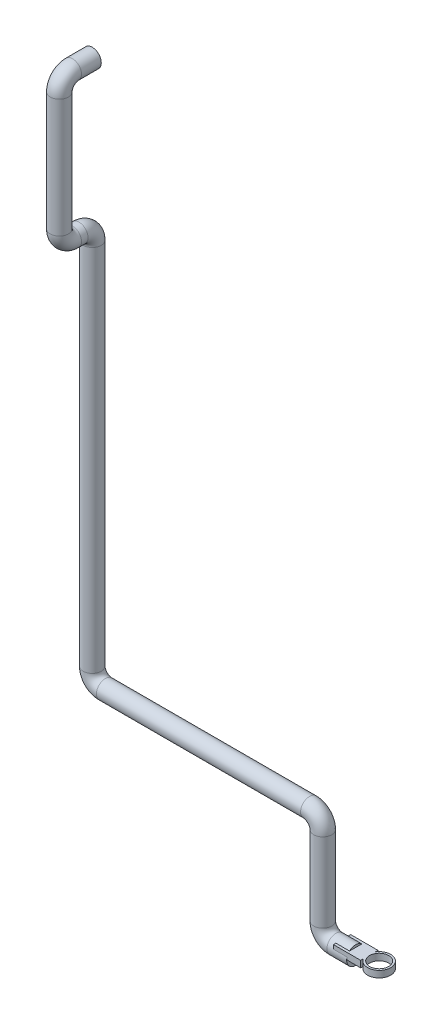
SolidWorks part; units mm, degrees
ref_plane "Alzado" through (0, 0, 0) normal (0, 0, 1) x (1, 0, 0)
ref_plane "Planta" through (0, 0, 0) normal (0, 1, 0) x (1, 0, 0)
ref_plane "Vista lateral" through (0, 0, 0) normal (1, 0, 0) x (0, 0, -1)
sketch3d "Croquis3D1"
  line L0 (0, 0, 0) -> (-30, 0, 0)
  line L1 (-50, 20, 0) -> (-50, 140, 0)
  line L2 (-70, 160, 0) -> (-380, 160, 0)
  line L3 (-400, 180, 0) -> (-400, 740, 0)
  line L4 (-400, 760, 20) -> (-400, 760, 30)
  line L5 (-400, 780, 50) -> (-400, 960, 50)
  line L6 (-400, 980, 30) -> (-400, 980, 0)
  arc A0 (-400, 960, 50) -> (-400, 980, 30) centre (-400, 960, 30) ccw
  arc A1 (-400, 760, 30) -> (-400, 780, 50) centre (-400, 780, 30) ccw
  arc A2 (-400, 740, 0) -> (-400, 760, 20) centre (-400, 740, 20) ccw
  arc A3 (-380, 160, 0) -> (-400, 180, 0) centre (-380, 180, 0) ccw
  arc A4 (-50, 140, 0) -> (-70, 160, 0) centre (-70, 140, 0) ccw
  arc A5 (-30, 0, 0) -> (-50, 20, 0) centre (-30, 20, 0) ccw
  point P12 (-400, 980, 50)
  point P13 (-420, 960, 30)
  point P16 (-400, 760, 50)
  point P17 (-420, 780, 30)
  point P20 (-400, 760, 0)
  point P21 (-380, 740, 20)
  point P24 (-400, 160, 0)
  point P25 (-380, 180, -20)
  point P28 (-50, 160, 0)
  point P29 (-70, 140, 20)
  point P32 (-50, 0, 0)
  point P33 (-30, 20, -20)
  dimension "D8" = 20
  dimension "D1" = 50
  dimension "D2" = 160
  dimension "D3" = 350
  dimension "D4" = 600
  dimension "D5" = 50
  dimension "D6" = 220
  dimension "D7" = 50
sketch "Croquis1" plane through (0, 0, 0) normal (1, 0, 0) x (0, 0, -1)
  circle A0 centre (0, 0) radius 13.7
  dimension "D1" = 27.4
sweep "Barrer1" add profiles "Croquis1" path "Croquis3D1"
sketch "Croquis2" plane through (0, 0, 0) normal (0, 1, 0) x (1, 0, 0)
  line L0 (0, 0) -> (35.5974, 0) construction
  line L1 (0, -13.7) -> (0, 13.7) construction
  line L2 (20.7289, -9.2292) -> (20.7289, -13.132)
  line L3 (-20.7289, 13.132) -> (20.7289, 13.132)
  line L4 (-20.7289, 13.132) -> (-20.7289, -13.132)
  line L5 (-20.7289, -13.132) -> (20.7289, -13.132)
  line L6 (20.7289, 13.132) -> (20.7289, 9.2292)
  line L7 (-20.7289, 13.132) -> (20.7289, -13.132) construction
  line L8 (-20.7289, -13.132) -> (20.7289, 13.132) construction
  circle A0 centre (35.5974, 0) radius 17.5
  circle A1 centre (35.5974, 0) radius 14.466
  dimension "D1" = 35
extrude "Saliente-Extruir1" add sketch "Croquis2" along normal blind 10 contours A0 L6 L3 L4 L5 L2 | A0 A1
